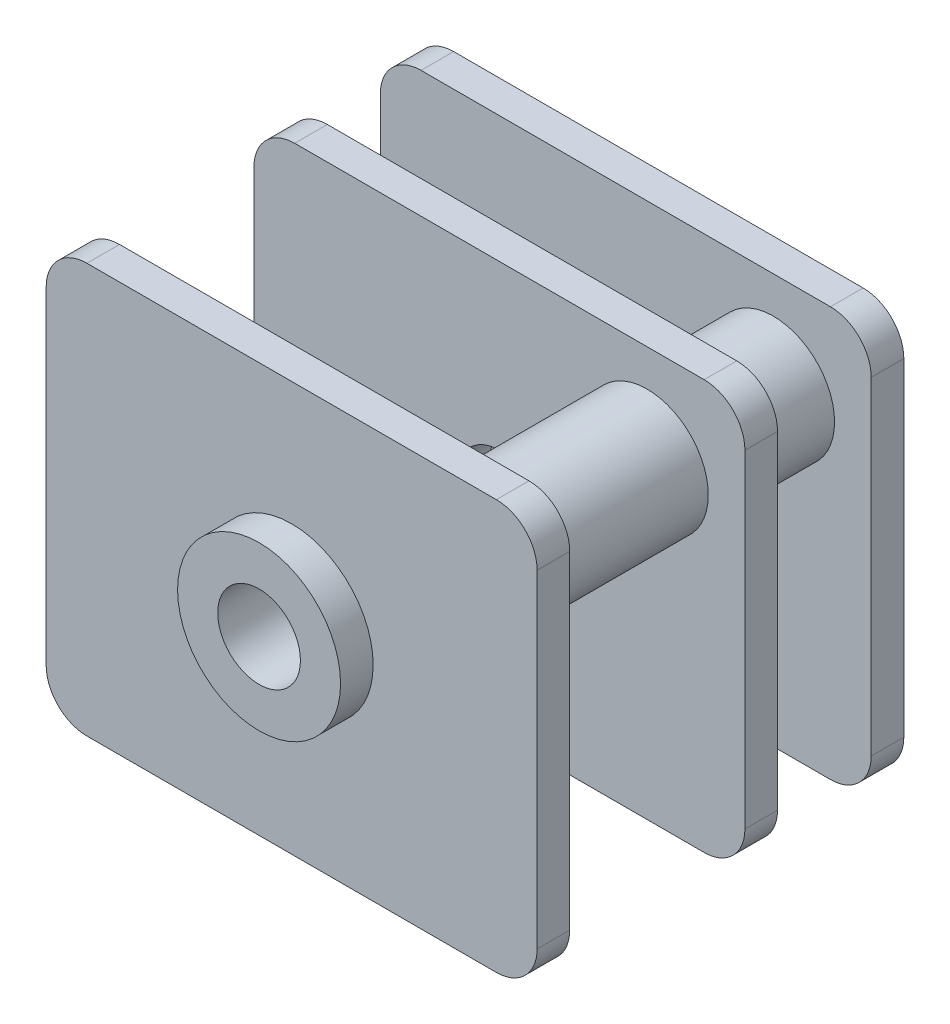
SolidWorks part; units mm, degrees
ref_plane "Horní rovina" through (0, 0, 0) normal (0, 0, 1) x (1, 0, 0)
ref_plane "Přední rovina" through (0, 0, 0) normal (0, 1, 0) x (1, 0, 0)
ref_plane "Pravá rovina" through (0, 0, 0) normal (1, 0, 0) x (0, 0, -1)
sketch "Skica5" plane through (0, 0, 0) normal (0, 0, 1) x (1, 0, 0)
  line L5 (-6.025, 5.025) -> (6.025, 5.025)
  line L6 (-6.025, 5.025) -> (-6.025, -5.025)
  line L7 (-6.025, -5.025) -> (6.025, -5.025)
  line L8 (6.025, 5.025) -> (6.025, -5.025)
  line L9 (-6.025, 5.025) -> (6.025, -5.025) construction
  line L10 (-6.025, -5.025) -> (6.025, 5.025) construction
  point P0 (0, 0)
  dimension "D1" = 10.05
  dimension "D2" = 12.05
extrude "Přidat vysunutím5" add sketch "Skica5" along normal blind 0.8 separate body
fillet "Zaoblit2" radius 1 4 edges at (-6.025, -5.025, 0.4) (-6.025, 5.025, 0.4) (6.025, -5.025, 0.4) (6.025, 5.025, 0.4)
sketch "Skica6" plane through (0, 0, 0.8) normal (0, 0, 1) x (1, 0, 0)
  line L2 (-6.025, 4.025) -> (-6.025, -4.025) construction
  line L4 (-5.025, -5.025) -> (5.025, -5.025) construction
  line L5 (6.025, -4.025) -> (6.025, 4.025) construction
  line L7 (5.025, 5.025) -> (-5.025, 5.025) construction
  circle A2 centre (3.625, 2.625) radius 1.5
  circle A5 centre (-3.625, -2.625) radius 1.5
  dimension "D1" = 3
  dimension "D2" = 3
  dimension "D3" = 2.4
  dimension "D4" = 2.4
  dimension "D5" = 2.4
  dimension "D6" = 2.4
extrude "Přidat vysunutím6" add sketch "Skica6" along normal blind 7.4
pattern_linear "LinPole1" count 2 spacing 3.1 along (0, 0, 1) of "Přidat vysunutím5", "Zaoblit2"
pattern_linear "LinPole2" count 2 spacing 8.2 along (0, 0, 1) of "Přidat vysunutím5", "Zaoblit2"
sketch "Skica7" plane through (0, 0, 9) normal (0, 0, 1) x (1, 0, 0)
  circle A4 centre (0, 0) radius 2
  circle A5 centre (0, 0) radius 1.015
  dimension "D1" = 4
  dimension "D2" = 2.03
extrude "Přidat vysunutím7" add sketch "Skica7" along normal blind 0.8
sketch "Skica9" plane through (0, 0, 0) normal (0, 0, 1) x (1, 0, 0)
  circle A1 centre (0, 0) radius 1.015 construction
  circle A4 centre (0, 0) radius 1.015
extrude "Odebrat vysunutím2" cut sketch "Skica9" along normal through all
